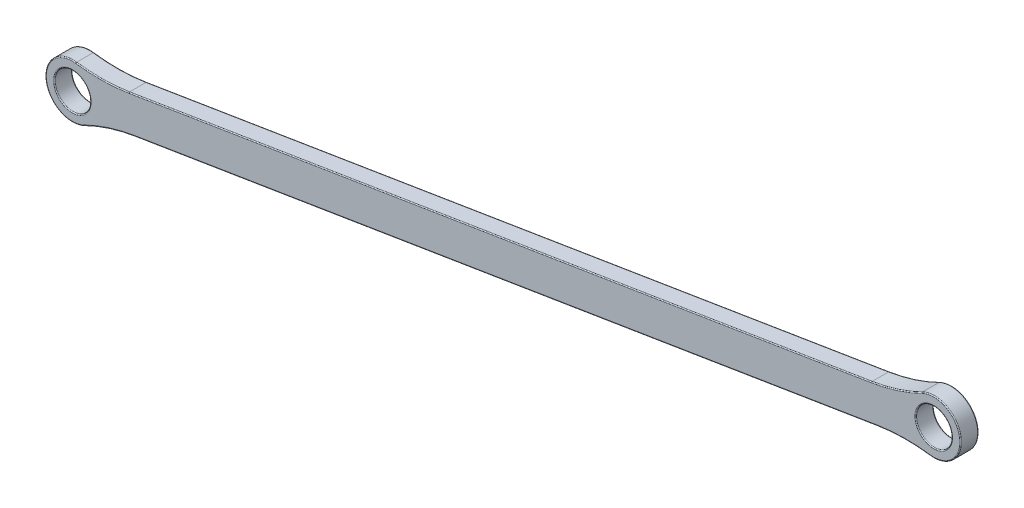
SolidWorks part; units mm, degrees
ref_plane "Front Plane" through (0, 0, 0) normal (0, 0, 1) x (1, 0, 0)
ref_plane "Top Plane" through (0, 0, 0) normal (0, 1, 0) x (1, 0, 0)
ref_plane "Right Plane" through (0, 0, 0) normal (1, 0, 0) x (0, 0, -1)
sketch "Sketch1" plane through (0, 0, 0) normal (0, 0, 1) x (1, 0, 0)
  line L0 (-86.7908, 226.3073) -> (-230.9032, 202.9067) construction
  line L1 (-86.7908, 226.3073) -> (-230.9032, 202.9067) construction
  line L2 (-230.9032, 202.9067) -> (-86.7908, 226.3073) construction
  line L3 (-231.3841, 205.8679) -> (-87.2716, 229.2686)
  line L4 (-230.4224, 199.9454) -> (-86.3099, 223.3461)
  arc A0 (-231.3841, 205.8679) -> (-230.4224, 199.9454) centre (-230.9032, 202.9067) ccw
  arc A1 (-86.3099, 223.3461) -> (-87.2716, 229.2686) centre (-86.7908, 226.3073) ccw
  circle A2 centre (-230.9032, 202.9067) radius 4.5
  circle A3 centre (-86.7908, 226.3073) radius 4.5
  arc A4 (-231.3841, 205.8679) -> (-230.4224, 199.9454) centre (-230.9032, 202.9067) cw
  arc A5 (-87.2716, 229.2686) -> (-86.3099, 223.3461) centre (-86.7908, 226.3073) ccw
  point P3 (-158.847, 214.607)
  dimension "D2" = 9
  dimension "D1" = 6
extrude "Boss-Extrude1" add sketch "Sketch1" against normal blind 3 contours L3 A2 L4 A0 | L3 A4 L4 A2 | A3 L3 A2 L4 | A5 L3 A3 L4 | L4 A3 L3 A1
fillet "Fillet1" radius 30 4 edges at (-90.5823, 228.731, -1.5) (-89.6207, 222.8085, -1.5) (-227.1117, 200.483, -1.5) (-228.0733, 206.4055, -1.5)
fillet "Fillet2" radius 0.15 20 edges at (-227.9032, 202.9067, -3) (-224.8037, 200.5256, -3) (-158.3662, 211.6458, -3) (-91.8235, 222.1187, -3) (-82.3489, 227.0286, -3) (-92.8903, 228.6884, -3) (-159.3278, 217.5682, -3) (-225.8705, 207.0953, -3) (-235.3451, 202.1854, -3) (-83.7908, 226.3073, -3) (-227.9032, 202.9067, 0) (-92.8903, 228.6884, 0) (-82.3489, 227.0286, 0) (-91.8235, 222.1187, 0) (-158.3662, 211.6458, 0) (-224.8037, 200.5256, 0) (-235.3451, 202.1854, 0) (-225.8705, 207.0953, 0) (-159.3278, 217.5682, 0) (-83.7908, 226.3073, 0)
